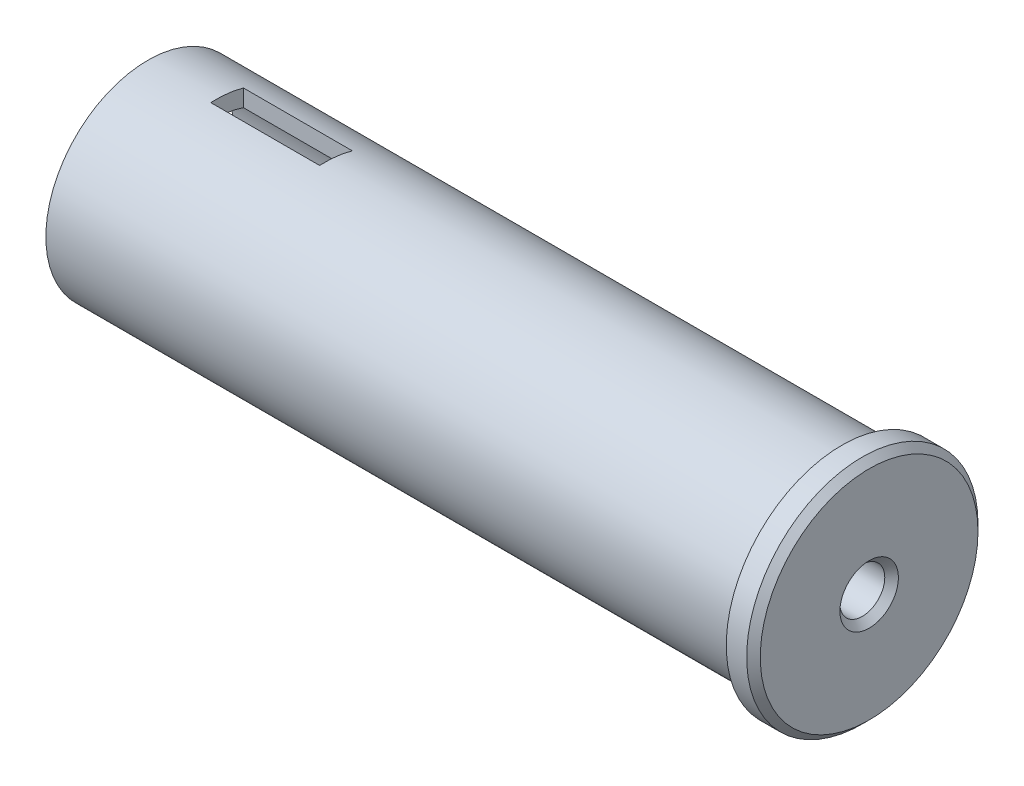
SolidWorks part; units mm, degrees
material "Custom Plastic"
ref_plane "Front Plane" through (0, 0, 0) normal (0, 0, 1) x (1, 0, 0)
ref_plane "Top Plane" through (0, 0, 0) normal (0, 1, 0) x (1, 0, 0)
ref_plane "Right Plane" through (0, 0, 0) normal (1, 0, 0) x (0, 0, -1)
sketch "Sketch2" plane through (0, 0, 0) normal (0, 1, 0) x (1, 0, 0)
  line L0 (0, 0) -> (-62.0809, 0) construction
  line L1 (0, 1.65) -> (-11, 1.65)
  line L2 (-11, 1.65) -> (-11, 6.3)
  line L3 (-11, 6.3) -> (-53, 6.3)
  line L7 (-53, 7.5) -> (-2, 7.5)
  line L8 (-2, 7.5) -> (-2, 8.5)
  line L9 (-2, 8.5) -> (0, 8.5)
  line L10 (0, 8.5) -> (0, 1.65)
  line L11 (-53, 7.5) -> (-53, 6.3)
  dimension "D1" = 3.3
  dimension "D2" = 15
  dimension "D3" = 1.2
  dimension "D4" = 2
  dimension "D5" = 1
  dimension "D6" = 51
  dimension "D7" = 11
revolve "Revolve1" add sketch "Sketch2" angle 360 about L0
chamfer "Chamfer2" distance 0.5 angle 45 2 edges at (0, 0, -1.65) (0, 0, -8.5)
sketch "Sketch3" plane through (0, 0, 0) normal (0, 1, 0) x (1, 0, 0)
  line L0 (-53, 7.5) -> (-53, -7.5) construction
  line L1 (-40, 2.0171) -> (-48, 2.0171)
  line L2 (-40, 2.0171) -> (-40, -0.3829)
  line L3 (-40, -0.3829) -> (-48, -0.3829)
  line L4 (-48, 2.0171) -> (-48, -0.3829)
  line L5 (-40, 2.0171) -> (-48, -0.3829) construction
  line L6 (-40, -0.3829) -> (-48, 2.0171) construction
  point P0 (-44, 0.8171)
  dimension "D1" = 2.4
  dimension "D2" = 8
  dimension "D3" = 5
extrude "Cut-Extrude1" cut sketch "Sketch3" against normal through all and the other way through all
equation "\"y-cross-rib-thickness\"=6"
equation "\"y-rib-thickness\"=6"
equation "\"bed-plate-thickness\"=6"
equation "\"x-plate-thickness\"=5"
equation "\"rod-diameter\"=12"
equation "\"t-nut-hole-diameter\"=3"
equation "\"y-plate-thickness\"=5"
equation "\"enclosure-thickness\"=0.6"
equation "\"M3-Clearance\"=3.3"
equation "\"M4-Clearance\"=4.3"
equation "\"M5-Clearance\"=5.3"
equation "\"M6-Clearance\"=6.3"
equation "\"M8-Clearance\"=8.3"
equation "\"623-Bearing-Dia\"=11.2"
